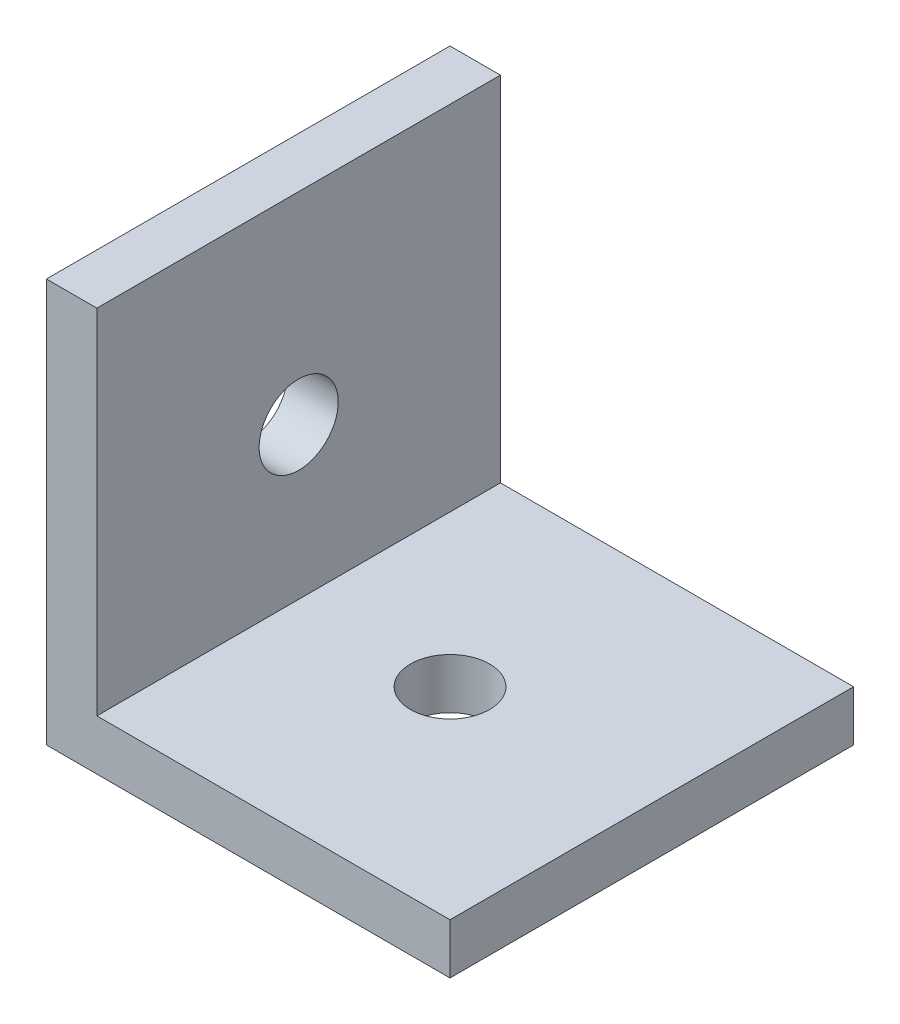
SolidWorks part; units mm, degrees
ref_plane "Front Plane" through (0, 0, 0) normal (0, 0, 1) x (1, 0, 0)
ref_plane "Top Plane" through (0, 0, 0) normal (0, 1, 0) x (1, 0, 0)
ref_plane "Right Plane" through (0, 0, 0) normal (1, 0, 0) x (0, 0, -1)
sketch "Sketch1" plane through (0, 0, 0) normal (0, 0, 1) x (1, 0, 0)
  line L0 (0, 0) -> (0, 25.4)
  line L2 (0, 0) -> (25.4, 0)
  dimension "D1" = 25.4
extrude "Extrude-Thin1" add sketch "Sketch1" against normal blind 25.4 thin
sketch "Sketch2" plane through (0, 0, 0) normal (0, -1, 0) x (1, 0, 0)
  line L0 (12.7, 0) -> (12.7, -12.7) construction
  line L1 (0, 0) -> (25.4, 0) construction
  line L2 (12.7, -12.7) -> (25.4, -12.7) construction
  line L3 (25.4, -25.4) -> (25.4, 0) construction
  circle A0 centre (12.7, -12.7) radius 2.4892
  dimension "D1" = 4.9784
extrude "Cut-Extrude1" cut sketch "Sketch2" against normal through all
ref_plane "Plane1" through (0, 0, 0) normal (0.7071, -0.7071, 0) x (0, 0, -1)
mirror "Mirror1" about plane through (0, 0, 0) normal (0.7071, -0.7071, 0) of "Cut-Extrude1"
equation "\"Thick\"= \"in\""
